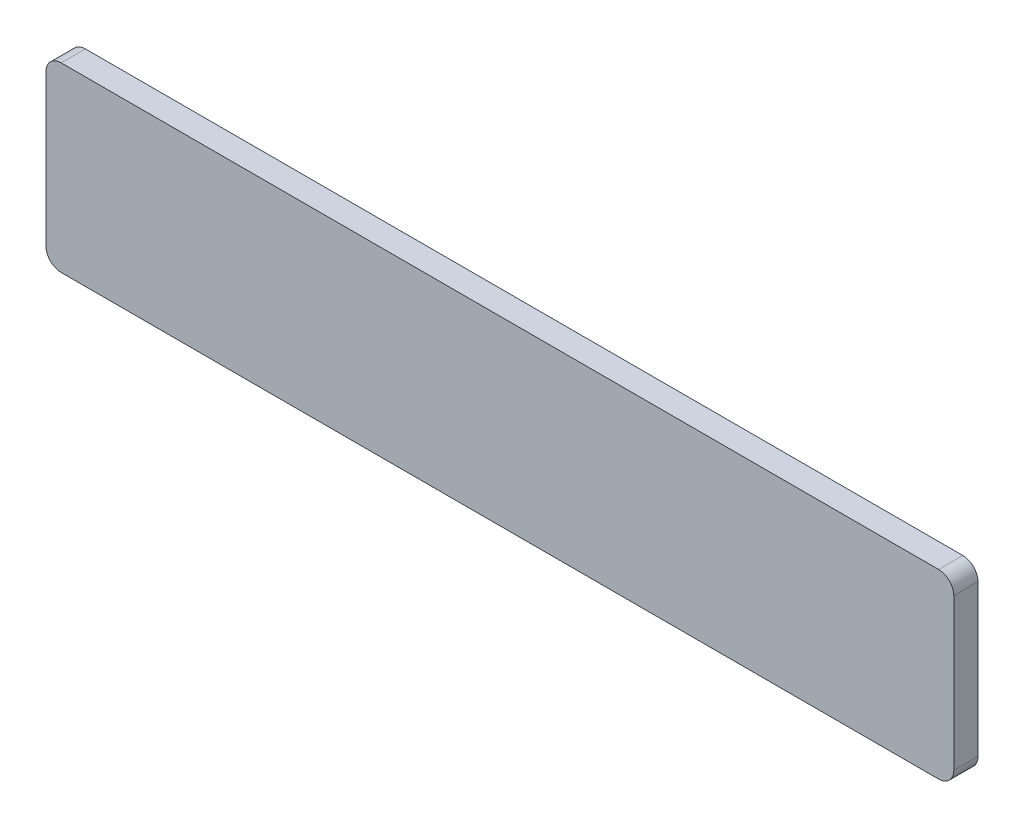
SolidWorks part; units mm, degrees
ref_plane "Front Plane" through (0, 0, 0) normal (0, 0, 1) x (1, 0, 0)
ref_plane "Top Plane" through (0, 0, 0) normal (0, 1, 0) x (1, 0, 0)
ref_plane "Right Plane" through (0, 0, 0) normal (1, 0, 0) x (0, 0, -1)
sketch "Sketch2" plane through (0, 0, 0) normal (0, 0, 1) x (1, 0, 0)
  line L1 (0.5, 0) -> (29.5, 0)
  line L2 (0, 0.5) -> (0, 5.5)
  line L3 (0.5, 6) -> (29.5, 6)
  line L4 (30, 0.5) -> (30, 5.5)
  arc A0 (29.5, 0) -> (30, 0.5) centre (29.5, 0.5) ccw
  arc A1 (29.5, 6) -> (30, 5.5) centre (29.5, 5.5) cw
  arc A2 (0, 5.5) -> (0.5, 6) centre (0.5, 5.5) cw
  arc A3 (0.5, 0) -> (0, 0.5) centre (0.5, 0.5) cw
  point P13 (0, 0)
extrude "Boss-Extrude2" add sketch "Sketch2" along normal blind 0.8
